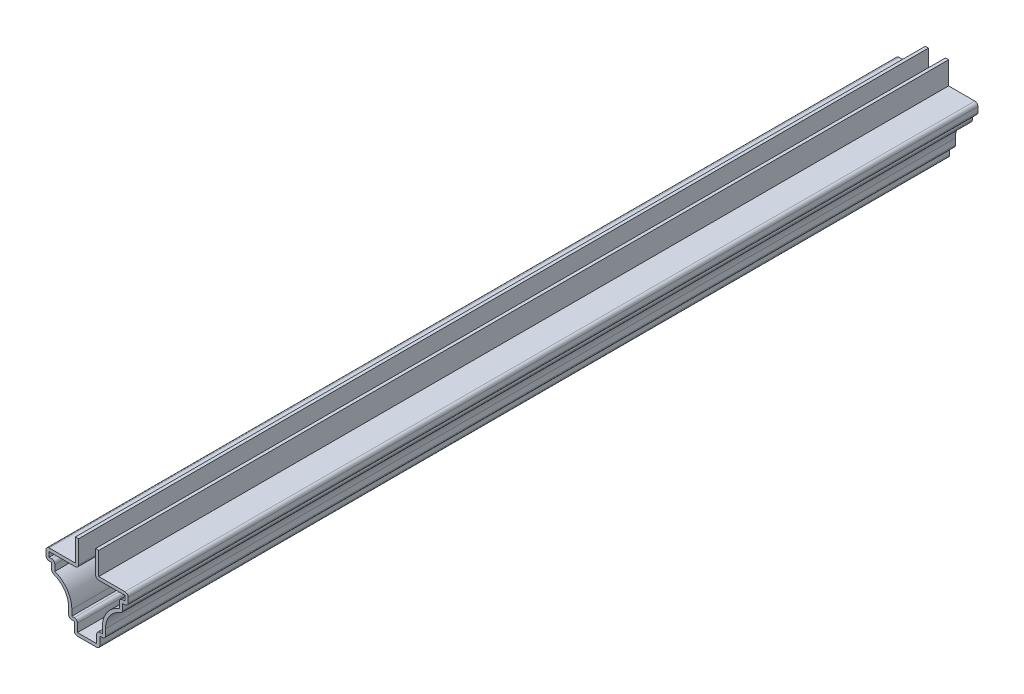
SolidWorks part; units mm, degrees
ref_plane "Front Plane" through (0, 0, 0) normal (0, 0, 1) x (1, 0, 0)
ref_plane "Top Plane" through (0, 0, 0) normal (0, 1, 0) x (1, 0, 0)
ref_plane "Right Plane" through (0, 0, 0) normal (1, 0, 0) x (0, 0, -1)
sketch "Sketch1" plane through (0, 0, 0) normal (0, 0, 1) x (1, 0, 0)
  line L0 (0, 0) -> (0, 22.4728) construction
  line L1 (3.5719, 0) -> (-3.5719, 0)
  line L2 (-3.5719, 0) -> (-3.5719, 3.175)
  line L3 (-3.5719, 3.175) -> (-5.1594, 3.175)
  line L4 (-5.1594, 3.175) -> (-5.1594, 5.7579)
  line L5 (-9.9219, 11.9062) -> (-9.9219, 14.2875)
  line L6 (-9.9219, 14.2875) -> (-11.5094, 14.2875)
  line L7 (-11.5094, 14.2875) -> (-11.5094, 17.4625)
  line L8 (-11.5094, 17.4625) -> (-3.2703, 17.4625)
  line L9 (-3.2703, 17.4625) -> (-3.2703, 23.8125)
  line L10 (3.2703, 17.4625) -> (3.2703, 23.8125)
  line L11 (11.5094, 17.4625) -> (3.2703, 17.4625)
  line L12 (11.5094, 14.2875) -> (11.5094, 17.4625)
  line L13 (9.9219, 14.2875) -> (11.5094, 14.2875)
  line L14 (9.9219, 11.9062) -> (9.9219, 14.2875)
  line L15 (5.1594, 3.175) -> (5.1594, 5.7579)
  line L16 (3.5719, 3.175) -> (5.1594, 3.175)
  line L17 (3.5719, 0) -> (3.5719, 3.175)
  arc A0 (-5.1594, 5.7579) -> (-9.9219, 11.9062) centre (-11.5094, 5.7579) ccw
  arc A1 (5.1594, 5.7579) -> (9.9219, 11.9062) centre (11.5094, 5.7579) cw
  point P9 (-2.2618, 0)
  point P15 (-6.4407, 6.6601)
  dimension "D9" = 6.35
  dimension "D1" = 23.8125
  dimension "D2" = 23.0188
  dimension "D3" = 6.35
  dimension "D4" = 3.175
  dimension "D5" = 2.3813
  dimension "D6" = 3.175
  dimension "D7" = 7.1437
  dimension "D8" = 1.5875
  dimension "D10" = 1.5875
  dimension "D11" = 8.2391
extrude "Extrude-Thin1" add sketch "Sketch1" against normal blind 238.125 thin
fillet "Fillet1" radius 0.889 16 edges at (-5.1594, 3.175, -119.0625) (-2.6829, 4.064, -119.0625) (-3.5719, 0, -119.0625) (3.5719, 0, -119.0625) (2.6829, 4.064, -119.0625) (5.1594, 3.175, -119.0625) (9.9219, 11.9062, -119.0625) (9.0329, 15.1765, -119.0625) (11.5094, 14.2875, -119.0625) (11.5094, 17.4625, -119.0625) (2.3813, 16.5735, -119.0625) (-9.9219, 11.9062, -119.0625) (-9.0329, 15.1765, -119.0625) (-11.5094, 14.2875, -119.0625) (-11.5094, 17.4625, -119.0625) (-2.3813, 16.5735, -119.0625)
